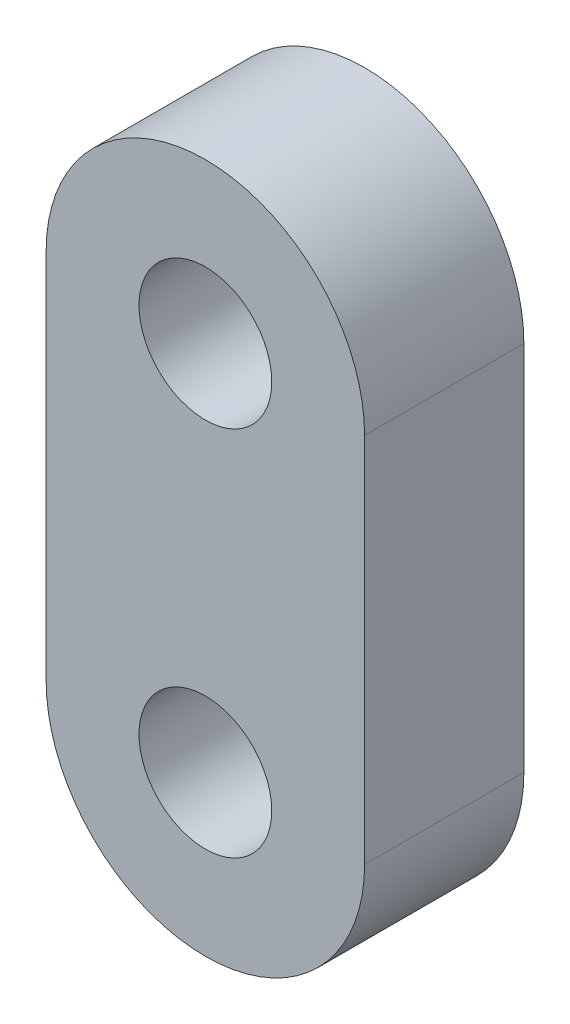
SolidWorks part; units mm, degrees
ref_plane "Front Plane" through (0, 0, 0) normal (0, 0, 1) x (1, 0, 0)
ref_plane "Top Plane" through (0, 0, 0) normal (0, 1, 0) x (1, 0, 0)
ref_plane "Right Plane" through (0, 0, 0) normal (1, 0, 0) x (0, 0, -1)
sketch "Sketch1" plane through (0, 0, 0) normal (0, 0, 1) x (1, 0, 0)
  line L0 (0, 21.9323) -> (0, -46.6526) construction
  line L1 (-3, 0) -> (-3, -7)
  line L2 (3, 0) -> (3, -7)
  line L4 (3, 21.9323) -> (3, -46.6526) construction
  line L5 (-3, 21.9323) -> (-3, -46.6526) construction
  arc A0 (3, 0) -> (-3, 0) centre (0, 0) ccw
  arc A1 (-3, -7) -> (3, -7) centre (0, -7) ccw
  circle A2 centre (0, 0) radius 1.25
  circle A3 centre (0, -7) radius 1.25
  dimension "D4" = 2.5
  dimension "4" = 2.5
  dimension "D3" = 7
  dimension "3.5" = 3
  dimension "D2" = 3
extrude "Boss-Extrude1" add sketch "Sketch1" along normal blind 3
